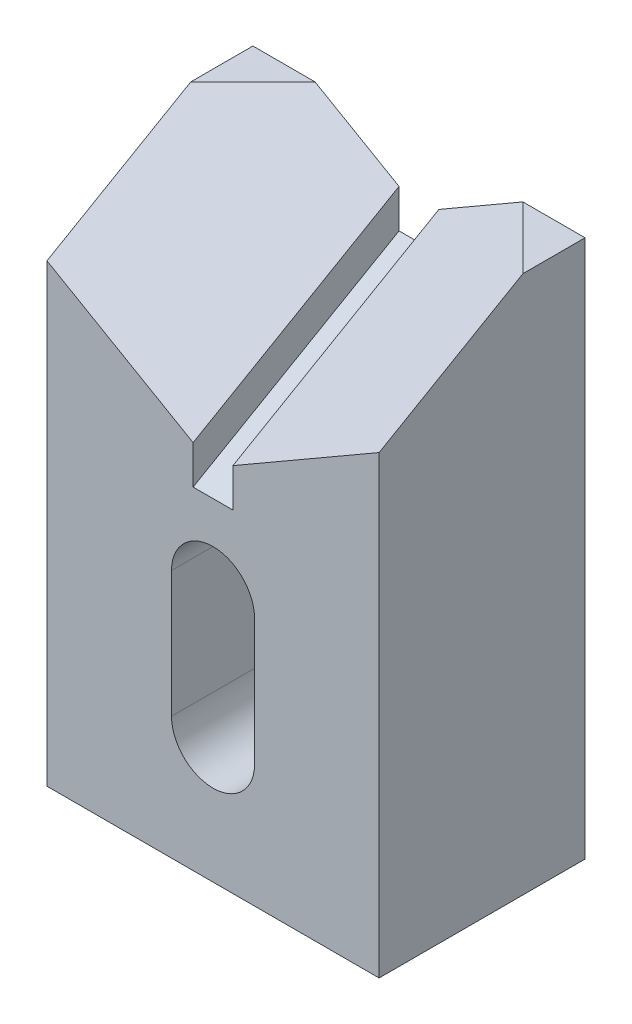
SolidWorks part; units mm, degrees
ref_plane "Front Plane" through (0, 0, 0) normal (0, 0, 1) x (1, 0, 0)
ref_plane "Top Plane" through (0, 0, 0) normal (0, 1, 0) x (1, 0, 0)
ref_plane "Right Plane" through (0, 0, 0) normal (1, 0, 0) x (0, 0, -1)
sketch "Sketch1" plane through (0, 0, 0) normal (0, 0, 1) x (1, 0, 0)
  line L0 (0, 38.1) -> (0, 18.796) construction
  line L1 (-25.4, 0) -> (25.4, 0)
  line L2 (-25.4, 0) -> (-25.4, 82.296)
  line L3 (-25.4, 82.296) -> (25.4, 82.296)
  line L4 (25.4, 0) -> (25.4, 82.296)
  line L5 (6.35, 38.1) -> (6.35, 18.796)
  line L6 (-6.35, 38.1) -> (-6.35, 18.796)
  arc A0 (6.35, 38.1) -> (-6.35, 38.1) centre (0, 38.1) ccw
  arc A1 (-6.35, 18.796) -> (6.35, 18.796) centre (0, 18.796) ccw
  point P4 (0, 0)
  point P8 (0, 28.448)
  dimension "D1" = 50.8
  dimension "D2" = 82.296
  dimension "D3" = 12.7
  dimension "D4" = 19.304
  dimension "D5" = 38.1
extrude "Boss-Extrude1" add sketch "Sketch1" along normal blind 31.496
sketch "Sketch2" plane through (0, 0, 31.496) normal (0, 0, 1) x (1, 0, 0)
  line L0 (-25.4, 69.596) -> (-3.048, 56.6911)
  line L1 (-25.4, 82.296) -> (-25.4, 0) construction
  line L2 (-3.048, 56.6911) -> (-3.048, 50.8)
  line L3 (-3.048, 50.8) -> (3.048, 50.8)
  line L4 (0, 82.296) -> (0, 0) construction
  line L5 (25.4, 82.296) -> (-25.4, 82.296) construction
  line L6 (3.048, 56.6911) -> (3.048, 50.8)
  line L7 (25.4, 69.596) -> (3.048, 56.6911)
  line L8 (-25.4, 69.596) -> (-25.4, 82.296)
  line L9 (-25.4, 82.296) -> (25.4, 82.296)
  line L10 (25.4, 82.296) -> (25.4, 69.596)
  point P12 (0, 50.8)
  dimension "D1" = 12.7
  dimension "D2" = 31.496
  dimension "D3" = 3.048
  dimension "D4" = 120
sketch "Sketch3" plane through (25.4, 0, 0) normal (1, 0, 0) x (0, 0, -1)
  line L0 (-31.496, 64.1118) -> (0, 82.296)
  line L1 (-31.496, 69.596) -> (-31.496, 56.6911) construction
  line L2 (-31.496, 69.596) -> (-31.496, 56.6911) construction
  line L3 (-31.496, 82.296) -> (0, 82.296) construction
  line L4 (0, 0) -> (0, 82.296) construction
  dimension "D1" = 60
extrude "Cut-Extrude1" cut sketch "Sketch2" along direction (0, 0.5, -0.866) on the side against the normal up to surface (36.3684 mm away) contours L0 L2 L3 L6 L7 L10 L9 L8
